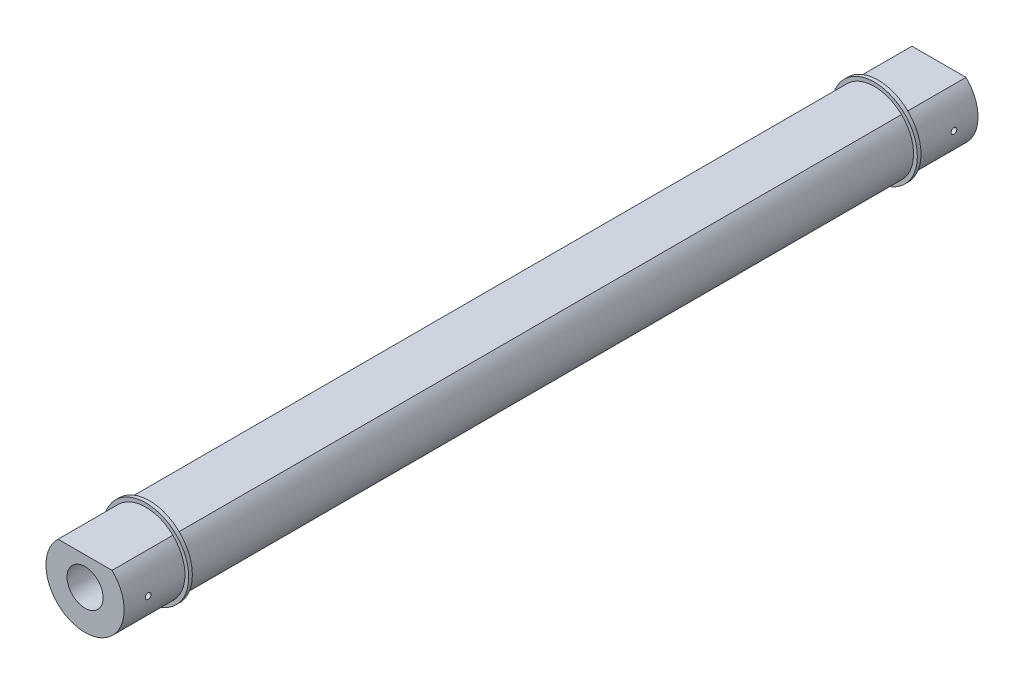
SolidWorks part; units mm, degrees
ref_plane "Front Plane" through (0, 0, 0) normal (0, 0, 1) x (1, 0, 0)
ref_plane "Top Plane" through (0, 0, 0) normal (0, 1, 0) x (1, 0, 0)
ref_plane "Right Plane" through (0, 0, 0) normal (1, 0, 0) x (0, 0, -1)
sketch "Sketch1" plane through (0, 0, 0) normal (0, 0, 1) x (1, 0, 0)
  line L0 (-7.1279, 7.4612) -> (7.1279, 7.4612)
  circle A0 centre (0, 0) radius 10.3187
  dimension "D1" = 20.6375
  dimension "D2" = 17.78
extrude "Rack" add sketch "Sketch1" along normal blind 112.7125 and the other way blind 112.7125 contours L0 A0
sketch "Sketch2" plane through (0, 0, 112.7125) normal (0, 0, 1) x (1, 0, 0)
  circle A0 centre (0, 0) radius 4.7625
  dimension "D1" = 9.525
extrude "End Hole" cut sketch "Sketch2" against normal blind 25.4
sketch "Sketch3" plane through (0, 0, 112.7125) normal (0, 0, 1) x (1, 0, 0)
  circle A0 centre (0, 0) radius 10.3187
  arc A1 (-7.1279, 7.4612) -> (7.1279, 7.4612) centre (0, 0) ccw construction
  circle A2 centre (0, 0) radius 11.3157
  dimension "D1" = 22.6314
extrude "Bump Stop" add sketch "Sketch3" along normal blind 0.9652 from offset 17.018 offset against normal yes
sketch "Sketch4" plane through (0, 0, 0) normal (1, 0, 0) x (0, 0, -1)
  line L0 (12.4473, 0) -> (-12.4473, 0) construction
  line L2 (-112.7125, 4.7625) -> (-112.7125, -4.7625) construction
  circle A0 centre (-106.3625, 0) radius 0.762
  dimension "D1" = 1.524
  dimension "D2" = 6.35
extrude "Safety Wire Hole" cut sketch "Sketch4" against normal through all both and the other way through all
mirror "Rack Mirror" about plane through (0, 0, 0) normal (0, 0, 1) of "Safety Wire Hole", "Bump Stop", "End Hole"
